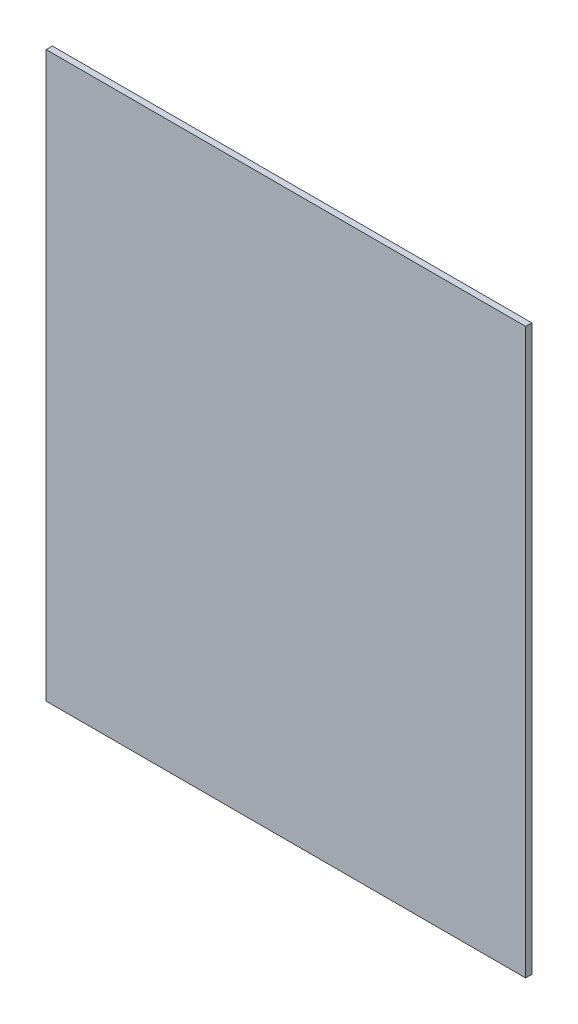
SolidWorks part; units mm, degrees
ref_plane "Plan de face" through (0, 0, 0) normal (0, 0, 1) x (1, 0, 0)
ref_plane "Plan de dessus" through (0, 0, 0) normal (0, 1, 0) x (1, 0, 0)
ref_plane "Plan de droite" through (0, 0, 0) normal (1, 0, 0) x (0, 0, -1)
sketch "Esquisse1" plane through (0, 0, 0) normal (0, 0, 1) x (1, 0, 0)
  line L1 (0, 0) -> (77.5, 0)
  line L2 (0, 0) -> (0, 91.2)
  line L3 (0, 91.2) -> (77.5, 91.2)
  line L4 (77.5, 0) -> (77.5, 91.2)
  dimension "D1" = 91.2
  dimension "D2" = 77.5
extrude "Boss.-Extru.1" add sketch "Esquisse1" along normal blind 1
sketch "Esquisse2" plane through (0, 0, 1) normal (0, 0, 1) x (1, 0, 0)
  line L0 (77.5, 91.2) -> (0, 91.2) construction
  line L1 (15, 22.2) -> (69, 22.2)
  line L2 (15, 22.2) -> (15, 108.2)
  line L3 (15, 108.2) -> (69, 108.2)
  line L4 (69, 22.2) -> (69, 108.2)
  line L5 (0, 91.2) -> (0, 0) construction
  dimension "D1" = 54
  dimension "D2" = 86
  dimension "D3" = 17
  dimension "D4" = 15
